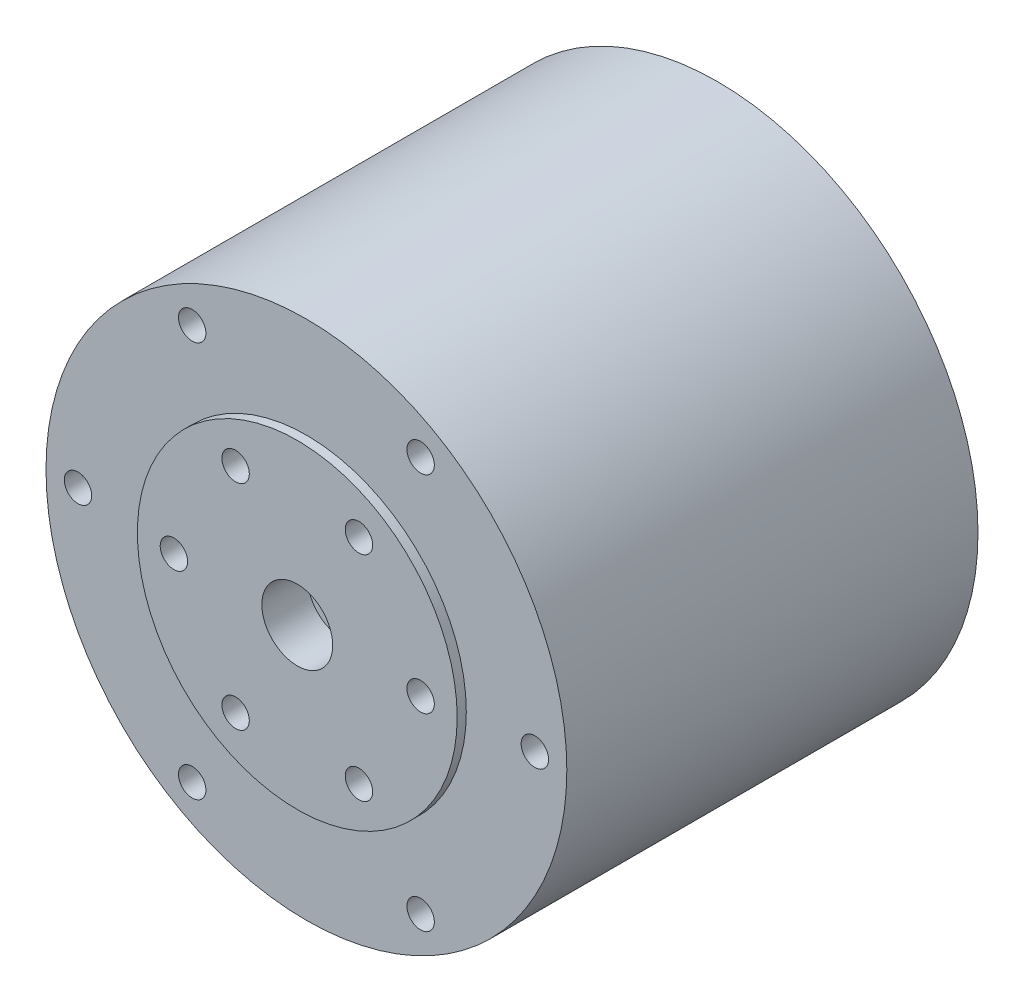
SolidWorks part; units mm, degrees
material "AISI 1010 钢，热轧条材"
ref_plane "前视基准面" through (0, 0, 0) normal (0, 0, 1) x (1, 0, 0)
ref_plane "上视基准面" through (0, 0, 0) normal (0, 1, 0) x (1, 0, 0)
ref_plane "右视基准面" through (0, 0, 0) normal (1, 0, 0) x (0, 0, -1)
sketch "草图1" plane through (0, 0, 0) normal (0, 0, 1) x (1, 0, 0)
  circle A0 centre (0, 0) radius 28.5
extrude "凸台-拉伸1" add sketch "草图1" along normal blind 45
sketch "草图2" plane through (0, 0, 0) normal (0, 0, -1) x (-1, 0, 0)
  line L0 (-44.9421, 0) -> (44.9421, 0) construction
  line L1 (0, -38.2286) -> (0, 38.2286) construction
  line L2 (13.435, 13.435) -> (0, 0) construction
  line L3 (0, 0) -> (-13.435, -13.435) construction
  line L4 (0, 0) -> (13.435, -13.435) construction
  line L5 (-13.435, 13.435) -> (0, 0) construction
  circle A0 centre (0, 0) radius 19 construction
  circle A1 centre (13.435, -13.435) radius 1.5
  circle A2 centre (-13.435, -13.435) radius 1.5
  circle A3 centre (-13.435, 13.435) radius 1.5
  circle A4 centre (13.435, 13.435) radius 1.5
  point P6 (0, 0)
  point P9 (0, 0)
  dimension "D1" = 45
  dimension "D2" = 45
  dimension "D3" = 45
  dimension "D4" = 45
extrude "切除-拉伸1" cut sketch "草图2" against normal blind 4
sketch "草图3" plane through (0, 0, 45) normal (0, 0, 1) x (1, 0, 0)
  line L0 (0, -32.3035) -> (0, 32.3035) construction
  line L1 (-12.5, -21.6506) -> (0, 0) construction
  line L2 (0, 0) -> (12.5, 21.6506) construction
  line L3 (0, 0) -> (12.5, -21.6506) construction
  line L4 (-12.5, 21.6506) -> (0, 0) construction
  line L5 (-46.1304, 0) -> (46.1304, 0) construction
  circle A0 centre (0, 0) radius 25 construction
  circle A3 centre (-12.5, -21.6506) radius 1.5
  circle A6 centre (-12.5, 21.6506) radius 1.5
  circle A7 centre (12.5, 21.6506) radius 1.5
  circle A8 centre (12.5, -21.6506) radius 1.5
  circle A9 centre (-25, 0) radius 1.5
  circle A10 centre (25, 0) radius 1.5
  point P6 (0, 0)
  point P9 (0, 0)
  point P12 (0, 0)
  point P15 (0, 0)
  point P24 (0, 0)
  dimension "D1" = 60
  dimension "D2" = 60
  dimension "D3" = 60
  dimension "D4" = 60
extrude "切除-拉伸2" cut sketch "草图3" against normal blind 5
sketch "草图4" plane through (0, 0, 45) normal (0, 0, 1) x (1, 0, 0)
  circle A0 centre (0, 0) radius 17.5
extrude "凸台-拉伸2" add sketch "草图4" along normal blind 1 contours A0
sketch "草图5" plane through (0, 0, 46) normal (0, 0, 1) x (1, 0, 0)
  line L0 (-40.9085, 0) -> (40.9085, 0) construction
  line L1 (-6.75, 11.6913) -> (0, 0) construction
  line L2 (0, 0) -> (6.75, -11.6913) construction
  line L3 (0, 0) -> (-6.75, -11.6913) construction
  line L4 (6.75, 11.6913) -> (0, 0) construction
  circle A0 centre (0, 0) radius 13.5 construction
  circle A1 centre (13.5, 0) radius 1.5
  circle A2 centre (-13.5, 0) radius 1.5
  circle A3 centre (6.75, 11.6913) radius 1.5
  circle A4 centre (-6.75, 11.6913) radius 1.5
  circle A5 centre (-6.75, -11.6913) radius 1.5
  circle A6 centre (6.75, -11.6913) radius 1.5
  circle A7 centre (0, 0) radius 3.8763
  point P6 (0, 0)
  dimension "D1" = 60
  dimension "D2" = 60
  dimension "D3" = 60
  dimension "D4" = 60
extrude "切除-拉伸3" cut sketch "草图5" against normal blind 5
